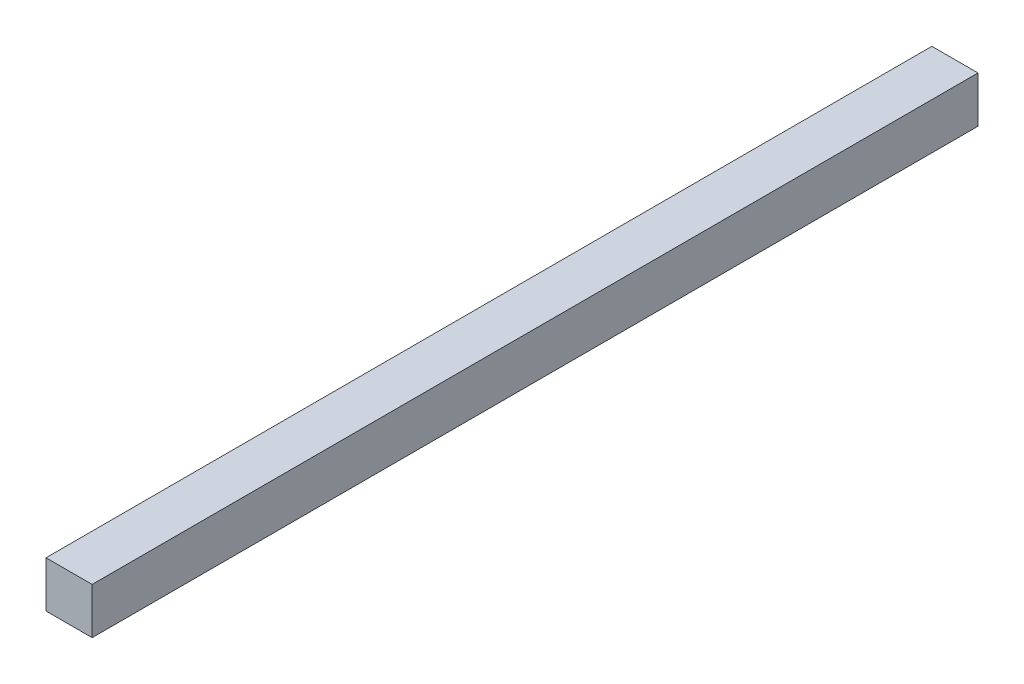
SolidWorks part; units mm, degrees
material "6061-T4 (SS)"
ref_plane "Front Plane" through (0, 0, 0) normal (0, 0, 1) x (1, 0, 0)
ref_plane "Top Plane" through (0, 0, 0) normal (0, 1, 0) x (1, 0, 0)
ref_plane "Right Plane" through (0, 0, 0) normal (1, 0, 0) x (0, 0, -1)
sketch "Sketch1" plane through (0, 0, 0) normal (0, 0, 1) x (1, 0, 0)
  line L1 (0, 0) -> (5, 0)
  line L2 (0, 0) -> (0, 5)
  line L3 (0, 5) -> (5, 5)
  line L4 (5, 0) -> (5, 5)
  dimension "D1" = 5
  dimension "D2" = 5
extrude "Boss-Extrude1" add sketch "Sketch1" along normal blind 96
sketch "Sketch2" plane through (0, 0, 0) normal (0, 1, 0) x (1, 0, 0)
  line L1 (0, 0) -> (96, 0)
  line L2 (0, 0) -> (0, -96)
  line L3 (0, -96) -> (96, -96)
  line L4 (96, 0) -> (96, -96)
  dimension "D1" = 96
  dimension "D2" = 96
extrude "Boss-Extrude2" [suppressed] add sketch "Sketch2" along normal blind 5
sketch "Sketch3" [suppressed] plane through (0, 0, 0) normal (0, -1, 0) x (1, 0, 0)
  line L0 (2.6746, 96) -> (2.6746, 0)
  line L1 (0, 96) -> (96, 96) construction
  line L2 (0, 0) -> (96, 0) construction
split line "Split Line1" [suppressed]
